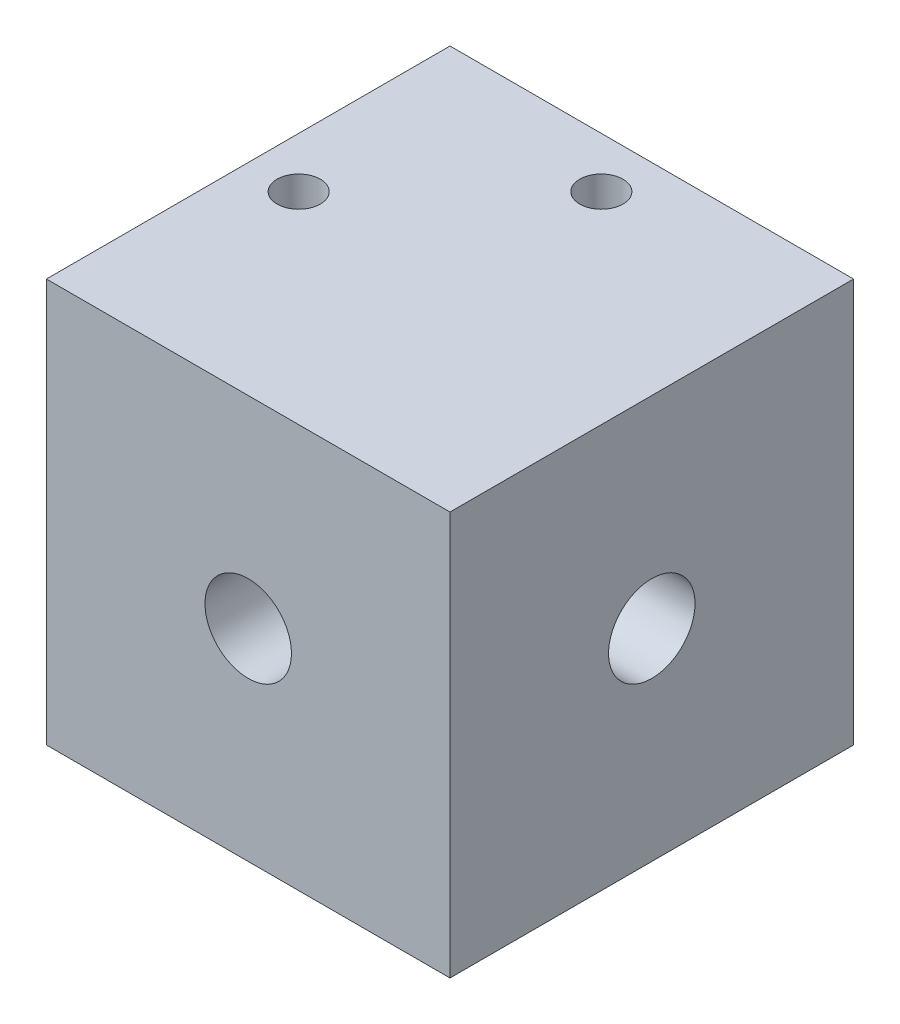
SolidWorks part; units mm, degrees
ref_plane "Alzado" through (0, 0, 0) normal (0, 0, 1) x (1, 0, 0)
ref_plane "Planta" through (0, 0, 0) normal (0, 1, 0) x (1, 0, 0)
ref_plane "Vista lateral" through (0, 0, 0) normal (1, 0, 0) x (0, 0, -1)
sketch "Croquis1" plane through (0, 0, 0) normal (0, 0, 1) x (1, 0, 0)
  line L1 (0, 0) -> (28, 0)
  line L2 (0, 0) -> (0, 28)
  line L3 (0, 28) -> (28, 28)
  line L4 (28, 0) -> (28, 28)
  dimension "D1" = 28
  dimension "D2" = 28
extrude "Saliente-Extruir1" add sketch "Croquis1" along normal blind 28
sketch "Croquis4" plane through (0, 0, 0) normal (-1, 0, 0) x (0, 0, 1)
  line L0 (14, 28) -> (14, 0) construction
  line L1 (28, 28) -> (0, 28) construction
  line L2 (28, 0) -> (0, 0) construction
  line L3 (0, 14) -> (28, 14) construction
  line L4 (0, 28) -> (0, 0) construction
  line L5 (28, 28) -> (28, 0) construction
  circle A0 centre (14, 14) radius 3.175
  dimension "D1" = 6.35
extrude "Cortar-Extruir3" cut sketch "Croquis4" against normal blind 10
sketch "Croquis6" plane through (28, 0, 0) normal (1, 0, 0) x (0, 0, -1)
  line L0 (-14, 28) -> (-14, 0) construction
  line L1 (-28, 28) -> (0, 28) construction
  line L2 (-28, 0) -> (0, 0) construction
  line L3 (-28, 14) -> (0, 14) construction
  line L4 (-28, 0) -> (-28, 28) construction
  line L5 (0, 0) -> (0, 28) construction
  circle A0 centre (-14, 14) radius 3
  dimension "D1" = 6
extrude "Cortar-Extruir4" cut sketch "Croquis6" against normal blind 10
sketch "Croquis8" plane through (0, 0, 0) normal (0, 0, -1) x (-1, 0, 0)
  circle A0 centre (-14, 14) radius 3.175
  dimension "D1" = 6.35
extrude "Cortar-Extruir5" cut sketch "Croquis8" against normal blind 10
sketch "Croquis9" plane through (0, 0, 28) normal (0, 0, 1) x (1, 0, 0)
  circle A0 centre (14, 14) radius 3
extrude "Cortar-Extruir6" cut sketch "Croquis9" against normal blind 10
sketch "Croquis10" plane through (0, 28, 0) normal (0, 1, 0) x (1, 0, 0)
  line L0 (0, -14) -> (28, -14) construction
  line L1 (0, 0) -> (28, 0)
  line L2 (0, 0) -> (0, -28)
  line L3 (0, -28) -> (28, -28)
  line L4 (28, 0) -> (28, -28)
  line L5 (14, 0) -> (14, -28) construction
  line L6 (14, 0) -> (14, -3.5) construction
  line L7 (0, -14) -> (3.5, -14) construction
  circle A0 centre (3.5, -14) radius 1.5
  circle A1 centre (14, -3.5) radius 1.5
  dimension "D1" = 3.5
  dimension "D2" = 3.5
extrude "Cortar-Extruir7" cut sketch "Croquis10" against normal blind 12 contours A1 | A0
